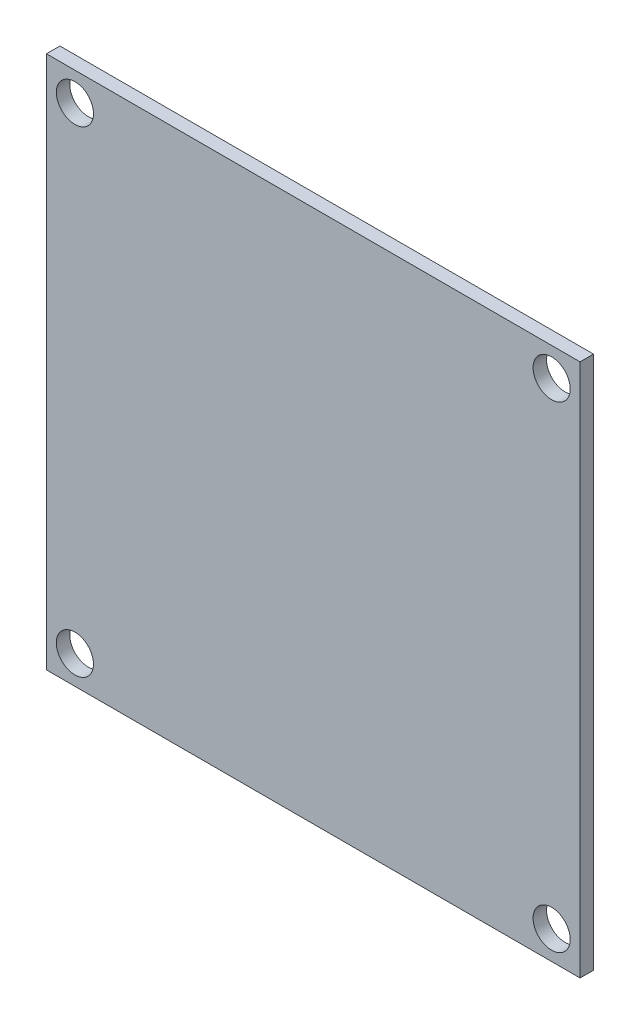
SolidWorks part; units mm, degrees
ref_plane "Front Plane" through (0, 0, 0) normal (0, 0, 1) x (1, 0, 0)
ref_plane "Top Plane" through (0, 0, 0) normal (0, 1, 0) x (1, 0, 0)
ref_plane "Right Plane" through (0, 0, 0) normal (1, 0, 0) x (0, 0, -1)
sketch "Sketch1" plane through (0, 0, 0) normal (0, 0, 1) x (1, 0, 0)
  line L1 (-25.1841, -25.1841) -> (25.1841, -25.1841)
  line L2 (-25.1841, -25.1841) -> (-25.1841, 25.1841)
  line L3 (-25.1841, 25.1841) -> (25.1841, 25.1841)
  line L4 (25.1841, -25.1841) -> (25.1841, 25.1841)
  line L5 (-25.1841, -25.1841) -> (25.1841, 25.1841) construction
  line L6 (-25.1841, 25.1841) -> (25.1841, -25.1841) construction
  line L7 (-22.5, -22.5) -> (22.5, -22.5) construction
  line L8 (-22.5, -22.5) -> (-22.5, 22.5) construction
  line L9 (-22.5, 22.5) -> (22.5, 22.5) construction
  line L10 (22.5, -22.5) -> (22.5, 22.5) construction
  line L11 (-22.5, -22.5) -> (22.5, 22.5) construction
  line L12 (-22.5, 22.5) -> (22.5, -22.5) construction
  circle A0 centre (-22.5, 22.5) radius 1.7526
  circle A1 centre (22.5, 22.5) radius 1.7526
  circle A2 centre (-22.5, -22.5) radius 1.7526
  circle A3 centre (22.5, -22.5) radius 1.7526
  point P0 (0, 0)
  point P6 (0, 0)
  dimension "D4" = 3.5052
  dimension "D1" = 50.3682
  dimension "D2" = 50.3682
  dimension "D3" = 45
extrude "Boss-Extrude1" add sketch "Sketch1" along normal blind 1.27
